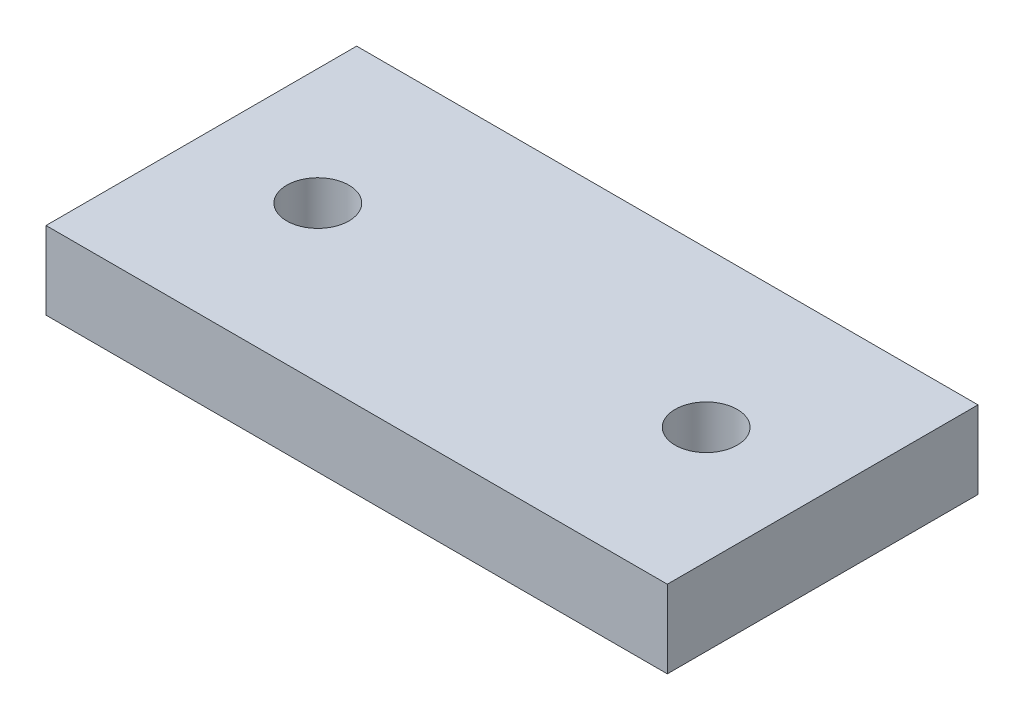
SolidWorks part; units mm, degrees
ref_plane "Front Plane" through (0, 0, 0) normal (0, 0, 1) x (1, 0, 0)
ref_plane "Top Plane" through (0, 0, 0) normal (0, 1, 0) x (1, 0, 0)
ref_plane "Right Plane" through (0, 0, 0) normal (1, 0, 0) x (0, 0, -1)
sketch "Sketch1" plane through (0, 0, 0) normal (0, 1, 0) x (1, 0, 0)
  line L1 (-20, -10) -> (20, -10)
  line L2 (-20, -10) -> (-20, 10)
  line L3 (-20, 10) -> (20, 10)
  line L4 (20, -10) -> (20, 10)
  point P5 (0, 0)
  dimension "D1" = 20
  dimension "D2" = 40
extrude "Boss-Extrude1" add sketch "Sketch1" along normal blind 5 contours L3 L4 L1 L2
sketch "Sketch2" plane through (0, 5, 0) normal (0, 1, 0) x (1, 0, 0)
  circle A0 centre (-12.5, 0) radius 2
  circle A1 centre (12.5, 0) radius 2
extrude "Cut-Extrude1" cut sketch "Sketch2" against normal blind 5
